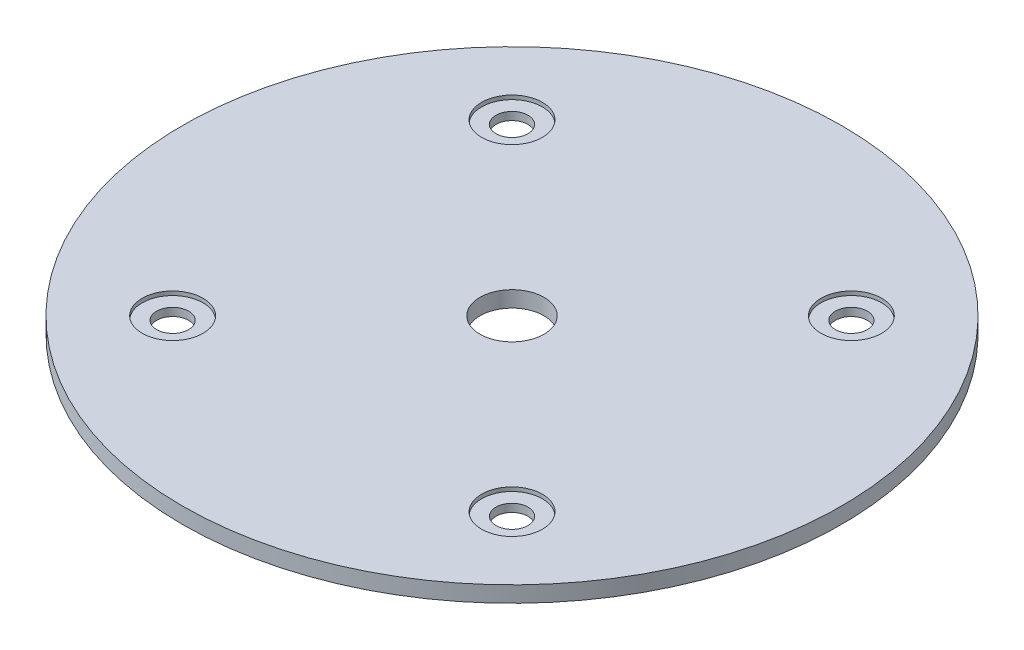
SolidWorks part; units mm, degrees
ref_plane "Front Plane" through (0, 0, 0) normal (0, 0, 1) x (1, 0, 0)
ref_plane "Top Plane" through (0, 0, 0) normal (0, 1, 0) x (1, 0, 0)
ref_plane "Right Plane" through (0, 0, 0) normal (1, 0, 0) x (0, 0, -1)
sketch "Sketch2" plane through (0, 0, 0) normal (0, 1, 0) x (1, 0, 0)
  circle A0 centre (0, 0) radius 65.405
  dimension "D1" = 130.81
extrude "Boss-Extrude1" add sketch "Sketch2" along normal mid plane 3.175
sketch "Sketch3" plane through (0, 1.5875, 0) normal (0, 1, 0) x (1, 0, 0)
  line L0 (-1000, 0) -> (49000, 0) construction
  line L1 (-33.676, -33.676) -> (33.676, 33.676) construction
  line L2 (33.676, 33.676) -> (0, 0) construction
  line L3 (-33.676, 33.676) -> (33.676, -33.676) construction
  point P9 (0, 0)
  point P19 (-33.676, 33.676)
  point P22 (33.676, 33.676)
  point P25 (33.676, -33.676)
  point P28 (-33.676, -33.676)
  dimension "D1" = 45
  dimension "D2" = 95.25
hole_wizard "1/4 (0.25) Diameter Hole1" positions "Sketch3" profile "Sketch7" hole size "1/4" standard "ANSI Inch"
sketch "Sketch7" plane through (-33.676, 1.5875, 33.676) normal (1, 0, 0) x (0, 0, 1)
  line L0 (0, 0) -> (0, 3.175)
  line L1 (0, 3.175) -> (3.175, 3.175)
  line L2 (3.175, 3.175) -> (3.175, 0)
  line L5 (3.175, 0) -> (0, 0)
  line L11 (0, -6.35) -> (0, 107.95) construction
  dimension "Thru Hole Dia." = 6.35
  dimension "Thru Hole Depth" = 3.175
sketch "Sketch8" plane through (0, 1.5875, 0) normal (0, 1, 0) x (1, 0, 0)
  point P0 (0, 0)
hole_wizard "1/2 (0.5) Diameter Hole1" positions "Sketch8" profile "Sketch9" hole size "1/2" standard "ANSI Inch" end condition through all
sketch "Sketch9" plane through (0, 1.5875, 0) normal (1, 0, 0) x (0, 0, 1)
  line L0 (0, 0) -> (0, 3.175)
  line L1 (0, 3.175) -> (6.35, 3.175)
  line L2 (6.35, 3.175) -> (6.35, 0)
  line L5 (6.35, 0) -> (0, 0)
  line L11 (0, -6.35) -> (0, 107.95) construction
  dimension "Thru Hole Dia." = 12.7
  dimension "Thru Hole Depth" = 3.175
sketch "Sketch10" plane through (0, 1.5875, 0) normal (0, 1, 0) x (1, 0, 0)
  circle A0 centre (-33.676, 33.676) radius 6.0325
  circle A1 centre (33.676, 33.676) radius 6.0325
  circle A2 centre (33.676, -33.676) radius 6.0325
  circle A3 centre (-33.676, -33.676) radius 6.0325
  dimension "D1" = 12.065
extrude "Cut-Extrude1" cut sketch "Sketch10" against normal blind 0.7937
mirror "Mirror1" about plane through (0, 0, 0) normal (0, 1, 0) of "Cut-Extrude1"
equation "\"AIRFRAME_OD\"= 5.15in"
equation "\"AIRFRAME_ID\"= 4.99in"
equation "\"FLAT_T\"= 0.125in"
equation "\"NOSE_EXP_L\"= 27in"
equation "\"NOSE_SHOULDER_L\"= 5in"
equation "\"MAIN_L\"= 30in"
equation "\"RECO_COUP_L\"= 10in"
equation "\"RECO_SWITCH_L\"= 2in"
equation "\"DROGUE_L\"= 20in"
equation "\"ATS_FORE_COUP_L\"= 5.5in"
equation "\"ATS_AFT_COUP_L\"= 4.5in"
equation "\"LOWER_L\"= 30in"
equation "\"FIN_N\"= 4"
equation "\"CR_AFT_X\"= 0.5in"
equation "\"CR_FORE_X\"= 9.25in"
equation "\"D1@Sketch2\"=\"AIRFRAME_OD\""
equation "\"D1@Boss-Extrude1\"=\"FLAT_T\""
equation "\"COUPLER_OD\"= 4.998in"
equation "\"COUPLER_ID\"= 4.85in"
equation "\"RECO_ROD_X\"= 3.5in"
equation "\"ATS_ROD_X\"= 3.75in"
equation "\"FIN_ROOT\"= 8in"
equation "\"FIN_X\"= 0.75in"
equation "\"MOTOR_OD\"= 3.091in"
equation "\"MOTOR_ID\"= 3.00in"
equation "\"MOTOR_L\"= 14in"
equation "\"MOTOR_LOWER_X\"= 2in"
equation "\"D2@Sketch3\"=\"ATS_ROD_X\""
